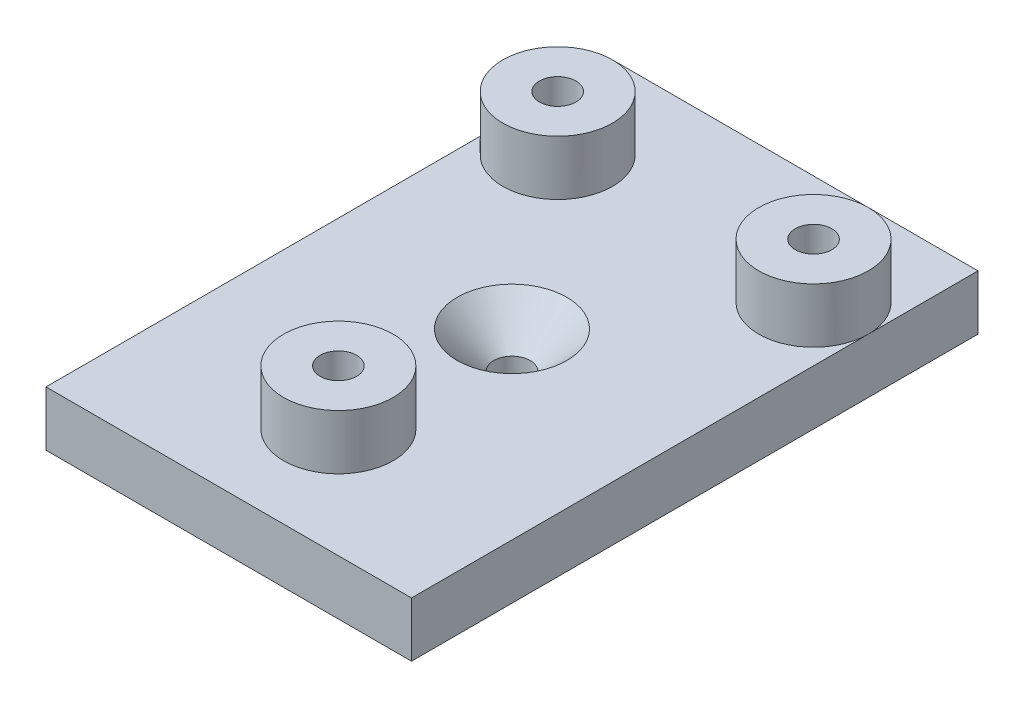
SolidWorks part; units mm, degrees
ref_plane "Спереди" through (0, 0, 0) normal (0, 0, 1) x (1, 0, 0)
ref_plane "Сверху" through (0, 0, 0) normal (0, 1, 0) x (1, 0, 0)
ref_plane "Справа" through (0, 0, 0) normal (1, 0, 0) x (0, 0, -1)
other "Configuration Table"
sketch "Эскиз1" plane through (0, 0, 0) normal (0, 1, 0) x (1, 0, 0)
  line L1 (-10.9436, 6.5826) -> (9.0564, 6.5826)
  line L2 (-10.9436, 6.5826) -> (-10.9436, -24.4174)
  line L3 (-10.9436, -24.4174) -> (9.0564, -24.4174)
  line L4 (9.0564, 6.5826) -> (9.0564, -24.4174)
  point P6 (11.2076, 1.807)
  point P7 (10.218, -3.1407)
  dimension "D1" = 20
  dimension "D2" = 31
extrude "Бобышка-Вытянуть1" add sketch "Эскиз1" along normal blind 3
sketch "Эскиз3" plane through (0, 3, 0) normal (0, 1, 0) x (1, 0, 0)
  line L0 (-10.9436, 0.5826) -> (9.0564, 0.5826) construction
  line L1 (-10.9436, 6.5826) -> (-10.9436, -24.4174) construction
  line L2 (9.0564, -24.4174) -> (9.0564, 6.5826) construction
  line L3 (9.0564, 6.5826) -> (-10.9436, 6.5826) construction
  line L4 (-9.9436, 6.5826) -> (-9.9436, -24.4174) construction
  line L5 (-10.9436, -24.4174) -> (9.0564, -24.4174) construction
  line L6 (-0.9436, 6.5826) -> (-0.9436, -24.4174) construction
  line L7 (8.0564, 6.5826) -> (8.0564, -24.4174) construction
  line L8 (-10.9436, -21.4174) -> (9.0564, -21.4174) construction
  circle A0 centre (-7.9436, 0.5826) radius 3
  circle A1 centre (-7.9436, 0.5826) radius 1
  circle A2 centre (6.0564, 0.5826) radius 1
  circle A3 centre (6.0564, 0.5826) radius 3
  circle A4 centre (-0.9436, -18.4174) radius 3
  circle A5 centre (-0.9436, -18.4174) radius 1
  dimension "D3" = 3
  dimension "D4" = 3
  dimension "D1" = 6
  dimension "D2" = 1
  dimension "D5" = 3
extrude "Бобышка-Вытянуть2" add sketch "Эскиз3" along normal blind 3
sketch "Эскиз4" plane through (0, 3, 0) normal (0, 1, 0) x (1, 0, 0)
  line L0 (9.0564, 6.5826) -> (-10.9436, 6.5826) construction
  line L1 (-0.9436, 6.5826) -> (-0.9436, -24.4174) construction
  line L2 (-10.9436, -24.4174) -> (9.0564, -24.4174) construction
  line L6 (9.0564, -24.4174) -> (9.0564, 0.5826) construction
  line L7 (9.0564, -8.9174) -> (-10.9436, -8.9174) construction
  line L8 (-10.9436, 0.5826) -> (-10.9436, -24.4174) construction
  circle A0 centre (-0.9436, -8.9174) radius 1
  dimension "D1" = 2
extrude "Вырез-Вытянуть1" cut sketch "Эскиз4" against normal blind 3
chamfer "Фаска1" distance 2 angle 45 1 edges at (-0.9436, 3, 9.9174)
